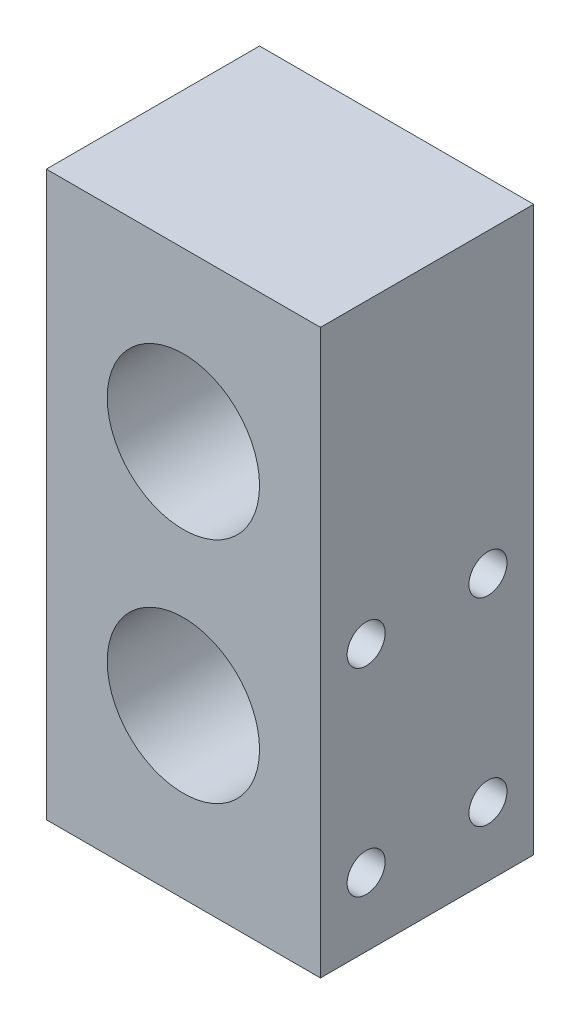
SolidWorks part; units mm, degrees
ref_plane "Front" through (0, 0, 0) normal (0, 0, 1) x (1, 0, 0)
ref_plane "Top" through (0, 0, 0) normal (0, 1, 0) x (1, 0, 0)
ref_plane "Right" through (0, 0, 0) normal (1, 0, 0) x (0, 0, -1)
sketch "Sketch2" plane through (0, 0, 0) normal (0, 1, 0) x (1, 0, 0)
  line L1 (-9, -7) -> (9, -7)
  line L2 (-9, -7) -> (-9, 7)
  line L3 (-9, 7) -> (9, 7)
  line L4 (9, -7) -> (9, 7)
  line L5 (-9, -7) -> (9, 7) construction
  line L6 (-9, 7) -> (9, -7) construction
  point P0 (0, 0)
  dimension "D1" = 18
  dimension "D2" = 14
extrude "Boss-Extrude1" add sketch "Sketch2" along normal blind 37
sketch "Sketch3" plane through (0, 0, 7) normal (0, 0, 1) x (1, 0, 0)
  line L0 (0, 0) -> (0, 11) construction
  line L1 (-9, 0) -> (9, 0) construction
  line L2 (0, 11) -> (0, 26) construction
  line L3 (-9, 37) -> (9, 37) construction
  circle A0 centre (0, 26) radius 5
  circle A1 centre (0, 11) radius 5
  point P8 (0, 21)
  point P9 (0, 16)
  dimension "D1" = 10
  dimension "D5" = 10
  dimension "D2" = 15
  dimension "D3" = 5
  dimension "D4" = 11
extrude "Cut-Extrude1" cut sketch "Sketch3" against normal through all
sketch "Sketch4" plane through (-9, 0, 0) normal (-1, 0, 0) x (0, 0, 1)
  line L0 (0, 0) -> (0, 11) construction
  line L1 (-4, 4.5) -> (4, 4.5) construction
  line L2 (-4, 4.5) -> (-4, 17.5) construction
  line L3 (-4, 17.5) -> (4, 17.5) construction
  line L4 (4, 4.5) -> (4, 17.5) construction
  line L5 (-4, 4.5) -> (4, 17.5) construction
  line L6 (-4, 17.5) -> (4, 4.5) construction
  line L7 (-7, 0) -> (7, 0) construction
  point P0 (0, 11)
  dimension "D1" = 4.5
  dimension "D2" = 13
  dimension "D3" = 8
hole_wizard "M3x0.5 Tapped Hole1" positions "3DSketch1" profile "Sketch5" tap size "M3x0.5" standard "ANSI Metric"
sketch3d "3DSketch1"
  point P0 (-9, 17.5, -4)
  point P3 (-9, 17.5, 4)
  point P6 (-9, 4.5, 4)
  point P9 (-9, 4.5, -4)
sketch "Sketch5" plane through (-9, 17.5, -4) normal (0, 1, 0) x (0, 0, 1)
  line L0 (0, 0) -> (0, 6.2511)
  line L1 (0, 6.2511) -> (1.25, 5.5)
  line L2 (1.25, 5.5) -> (1.25, 0)
  line L5 (1.25, 0) -> (0, 0)
  line L10 (0, 6.2511) -> (-1.25, 5.5) construction
  line L11 (0, -6.35) -> (0, 107.95) construction
  dimension "Tap Drill Dia." = 2.5
  dimension "Tap Drill Depth" = 5.5
  dimension "Drill Angle" = 118
cosmetic thread "Hole Thread1" parameters "D1"=5.5, "D2"=3
cosmetic thread "Hole Thread2" parameters "D1"=5.5, "D2"=3
cosmetic thread "Hole Thread3" parameters "D1"=5.5, "D2"=3
cosmetic thread "Hole Thread4" parameters "D1"=5.5, "D2"=3
mirror "Mirror1" about plane through (0, 0, 0) normal (1, 0, 0) of "M3x0.5 Tapped Hole1"
cosmetic thread "Hole Thread5" parameters "D1"=5.5, "D2"=3
cosmetic thread "Hole Thread6" parameters "D1"=5.5, "D2"=3
cosmetic thread "Hole Thread7" parameters "D1"=5.5, "D2"=3
cosmetic thread "Hole Thread8" parameters "D1"=5.5, "D2"=3
